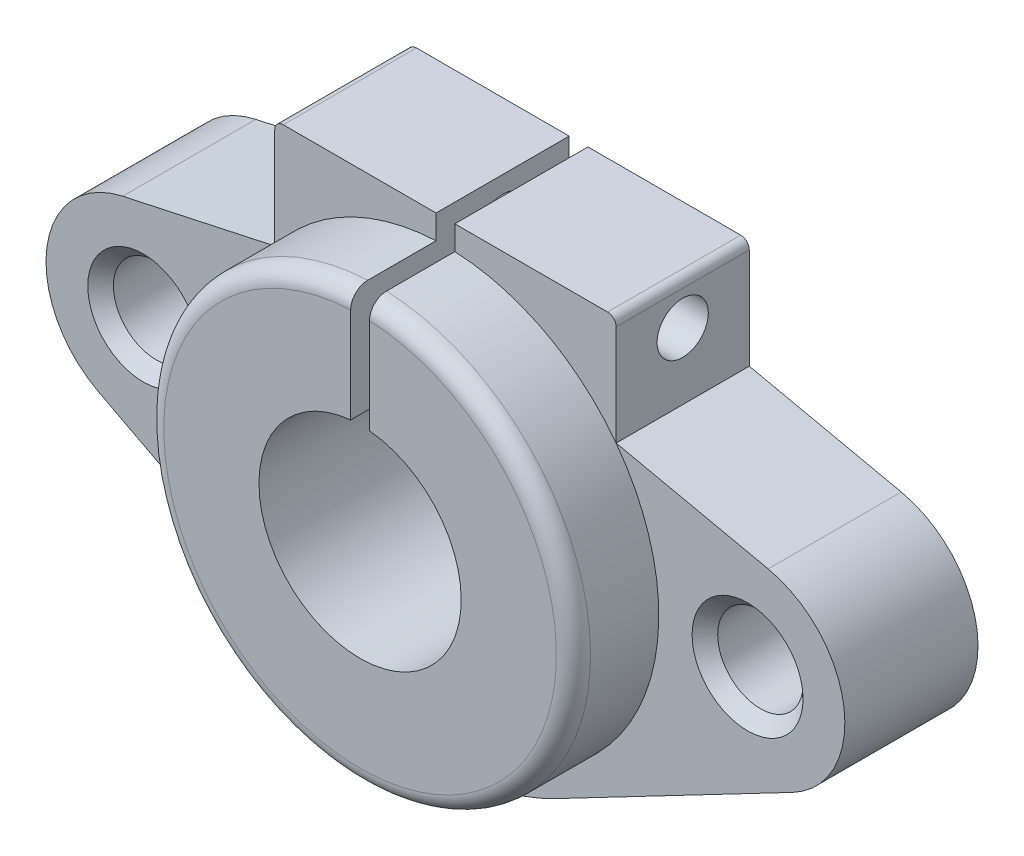
SolidWorks part; units mm, degrees
material "1060-H18"
ref_plane "Alzado" through (0, 0, 0) normal (0, 0, 1) x (1, 0, 0)
ref_plane "Planta" through (0, 0, 0) normal (0, 1, 0) x (1, 0, 0)
ref_plane "Vista lateral" through (0, 0, 0) normal (1, 0, 0) x (0, 0, -1)
sketch "Croquis1" plane through (0, 0, 0) normal (0, 0, 1) x (1, 0, 0)
  circle A0 centre (0, 0) radius 12.5
  circle A1 centre (0, 0) radius 5.925
  dimension "D1" = 25
  dimension "D2" = 11.85
extrude "Saliente-Extruir1" add sketch "Croquis1" along normal blind 12.8
sketch "Croquis2" plane through (0, 0, 0) normal (0, 0, -1) x (-1, 0, 0)
  line L0 (-17.7, 0) -> (17.7, 0) construction
  line L1 (-6.4395, -12.3184) -> (-20.3407, -5.0514)
  line L2 (6.4395, -12.3184) -> (20.3407, -5.0514)
  line L3 (0, 0) -> (0, 13.9) construction
  line L4 (-10, 13.9) -> (10, 13.9)
  line L5 (-10, 13.9) -> (-10, 7.5)
  line L6 (10, 13.9) -> (10, 7.5)
  line L7 (-10, 7.5) -> (-18.9066, 5.5708)
  line L8 (10, 7.5) -> (18.9066, 5.5708)
  circle A0 centre (0, 0) radius 13.9 construction
  circle A1 centre (-17.7, 0) radius 5.7 construction
  circle A2 centre (17.7, 0) radius 5.7 construction
  arc A3 (-6.4395, -12.3184) -> (6.4395, -12.3184) centre (0, 0) ccw
  circle A4 centre (0, 0) radius 12.5 construction
  arc A5 (-20.3407, -5.0514) -> (-18.9066, 5.5708) centre (-17.7, 0) cw
  arc A6 (18.9066, 5.5708) -> (20.3407, -5.0514) centre (17.7, 0) cw
  circle A7 centre (0, 0) radius 12.5 construction
  circle A8 centre (0, 0) radius 5.925 construction
  circle A9 centre (0, 0) radius 5.925
  point P4 (0, 0)
  point P19 (0, 13.9)
  dimension "D2" = 27.8
  dimension "D3" = 11.4
  dimension "D4" = 11.4
  dimension "D1" = 35.4
  dimension "D5" = 20
extrude "Saliente-Extruir2" add sketch "Croquis2" against normal blind 7.8
sketch "Croquis3" plane through (0, 0, 0) normal (0, 0, -1) x (-1, 0, 0)
  circle A0 centre (-17.7, 0) radius 2.5
  circle A1 centre (17.7, 0) radius 2.5
  point P0 (-17.7, 0)
  point P1 (17.7, 0)
  dimension "D1" = 5
extrude "Cortar-Extruir1" cut sketch "Croquis3" against normal up to vertex (7.8 mm away)
sketch "Croquis4" plane through (0, 0, 0) normal (0, 0, -1) x (-1, 0, 0)
  line L0 (0, 0) -> (0, 13.9) construction
  line L1 (10, 13.9) -> (-10, 13.9) construction
  line L2 (-0.55, 13.9) -> (0.55, 13.9)
  line L3 (0.55, 13.9) -> (0.55, 5.8994)
  line L4 (-0.55, 13.9) -> (-0.55, 5.8994)
  circle A0 centre (0, 0) radius 5.925 construction
  circle A1 centre (0, 0) radius 5.925 construction
  arc A2 (-0.55, 5.8994) -> (0.5766, 5.8969) centre (0, 0) cw
  point P10 (0, 13.9)
  line M7 (10, 13.9) -> (-10, 13.9)
  circle M15 centre (0, 0) radius 5.925
  dimension "D1" = 1.1
extrude "Cortar-Extruir2" cut sketch "Croquis4" against normal blind 13 contours L4 L3 M7 M15
fillet "Redondeo1" radius 1 1 edges at (0, -12.5, 12.8)
sketch "Croquis5" plane through (10, 0, 0) normal (1, 0, 0) x (0, 0, -1)
  line L0 (-7.8, 11.4) -> (0, 11.4) construction
  line L1 (-7.8, 13.9) -> (-7.8, 7.5) construction
  line L2 (0, 13.9) -> (0, 7.5) construction
  line L3 (-7.8, 13.9) -> (0, 13.9) construction
  circle A0 centre (-3.9, 11.4) radius 1.5
  dimension "D1" = 3
  dimension "D2" = 2.5
extrude "Cortar-Extruir3" cut sketch "Croquis5" against normal up to vertex
fillet "Redondeo2" radius 0.5 2 edges at (-10, 13.9, 3.9) (10, 13.9, 3.9)
chamfer "Chaflán1" distance 0.75 angle 45 2 edges at (-20.2, 0, 7.8) (15.2, 0, 7.8)
equation "\"D4@Croquis2\"=\"D3@Croquis2\""
